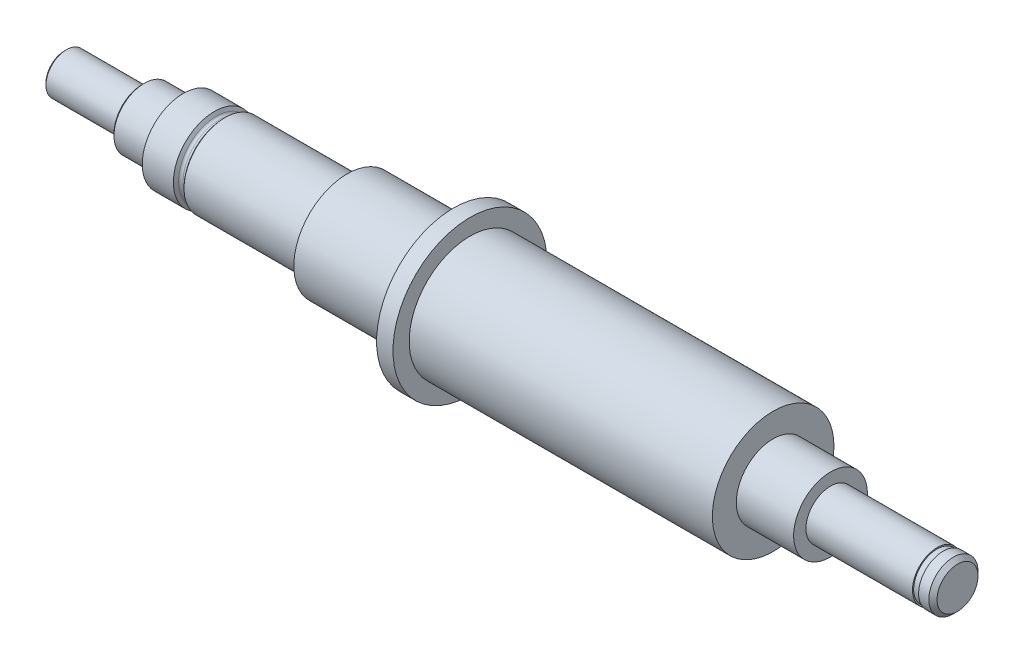
SolidWorks part; units mm, degrees
material "1.4006 (X10Cr13)"
ref_plane "Front Plane" through (0, 0, 0) normal (0, 0, 1) x (1, 0, 0)
ref_plane "Top Plane" through (0, 0, 0) normal (0, 1, 0) x (1, 0, 0)
ref_plane "Right Plane" through (0, 0, 0) normal (1, 0, 0) x (0, 0, -1)
ref_axis "Axis1" through (88.99, 0, 0) along (-1, 0, 0)
sketch "Sketch1" plane through (0, 0, 0) normal (0, 0, 1) x (1, 0, 0)
  line L1 (88.99, 0) -> (-88.99, 0) construction
  line L2 (-35, 5) -> (-31.2, 5)
  line L3 (-2, 6.5) -> (-2, 9.4)
  line L4 (-2, 9.4) -> (0, 9.4)
  line L5 (0, 9.4) -> (0, 7.42)
  line L6 (0, 7.42) -> (37, 7.42)
  line L7 (37, 7.42) -> (37, 4.5)
  line L8 (44, 3) -> (57, 3)
  line L9 (59.5, 2.5) -> (59.5, 0)
  line L10 (-49.5, 0) -> (59.5, 0)
  line L11 (44, 3) -> (44, 4.5)
  line L12 (44, 4.5) -> (37, 4.5)
  line L17 (-35, 5) -> (-35.433, 4.25)
  line L19 (-31.2, 5) -> (-30.9691, 4.6)
  line L20 (-30, 4.8) -> (-30, 4.9)
  line L21 (-30.6226, 4.4) -> (-30.4, 4.4)
  line L22 (-29.9, 5) -> (-15, 5)
  line L23 (-15, 5) -> (-15, 6.5)
  line L24 (-15, 6.5) -> (-2, 6.5)
  line L27 (-30, 4.9) -> (-29.9, 5)
  line L28 (59, 3) -> (59.5, 2.5)
  line L29 (-40, 2.5) -> (-49.25, 2.5)
  line L30 (-49.5, 2.25) -> (-49.5, 0)
  line L31 (-35.433, 4.25) -> (-35.433, 3.95)
  line L32 (-35.683, 3.7) -> (-39.75, 3.7)
  line L33 (-40, 3.45) -> (-40, 2.5)
  line L34 (-39.75, 3.7) -> (-40, 3.45)
  line L35 (-49.25, 2.5) -> (-49.5, 2.25)
  line L36 (57, 3) -> (57, 2.85)
  line L37 (57, 2.85) -> (57.75, 2.85)
  line L38 (57.75, 2.85) -> (57.75, 3)
  line L39 (57.75, 3) -> (59, 3)
  arc A1 (-30, 4.8) -> (-30.4, 4.4) centre (-30.4, 4.8) cw
  arc A2 (-30.9691, 4.6) -> (-30.6226, 4.4) centre (-30.6226, 4.8) ccw
  arc A3 (-35.683, 3.7) -> (-35.433, 3.95) centre (-35.683, 3.95) ccw
  point P4 (-40, 3.7)
  point P29 (-30.8536, 4.4)
  point P36 (-49.5, 2.5)
  dimension "D20" = 1.2
  dimension "D21" = 0.4
  dimension "D14" = 0.25
  dimension "D1" = 7.42
  dimension "D2" = 5
  dimension "D3" = 2
  dimension "D4" = 9.4
  dimension "D5" = 0.75
  dimension "D6" = 15
  dimension "D7" = 37
  dimension "D8" = 3
  dimension "D9" = 7
  dimension "D10" = 4.5
  dimension "D11" = 9.5
  dimension "D12" = 10
  dimension "D13" = 7.4
  dimension "D15" = 28
  dimension "D16" = 60
  dimension "D17" = 60
  dimension "D18" = 5
  dimension "D19" = 0.6
  dimension "D22" = 15
  dimension "D23" = 1.5
  dimension "D24" = 135
  dimension "D25" = 0.5
  dimension "D26" = 2.85
  dimension "D27" = 0.75
  dimension "D28" = 135
  dimension "D29" = 0.1
  dimension "D30" = 5
  dimension "D31" = 2.5
  dimension "D34" = 13
revolve "Revolve3" add sketch "Sketch1" angle 360 about axis through (88.99, 0, 0) along (-1, 0, 0)
cosmetic thread "Cosmetic Thread1" parameters "D2"=9.08
hole_wizard "M3 Tapped Hole1" positions "Sketch5" profile "Sketch6" tap size "M3" standard "ISO"
sketch "Sketch5" plane through (-49.5, 0, 0) normal (-1, 0, 0) x (0, 0, 1)
  point P0 (0, 0)
sketch "Sketch6" plane through (-49.5, 0, 0) normal (0, 1, 0) x (0, 0, 1)
  line L0 (0, 0) -> (0, 9.2511)
  line L1 (0, 9.2511) -> (1.25, 8.5)
  line L2 (1.25, 8.5) -> (1.25, 0.1588)
  line L3 (1.25, 0.1588) -> (1.525, 0)
  line L5 (1.525, 0) -> (0, 0)
  line L6 (-1.25, 0.1588) -> (-1.525, 0) construction
  line L10 (0, 9.2511) -> (-1.25, 8.5) construction
  line L11 (0, -6.35) -> (0, 107.95) construction
  dimension "Tap Drill Dia." = 2.5
  dimension "Tap Drill Depth" = 8.5
  dimension "Near C'Sink Dia." = 3.05
  dimension "Near C'Sink Angle" = 120
  dimension "Drill Angle" = 118
cosmetic thread "Hole Thread2" parameters "D1"=6, "D2"=3
